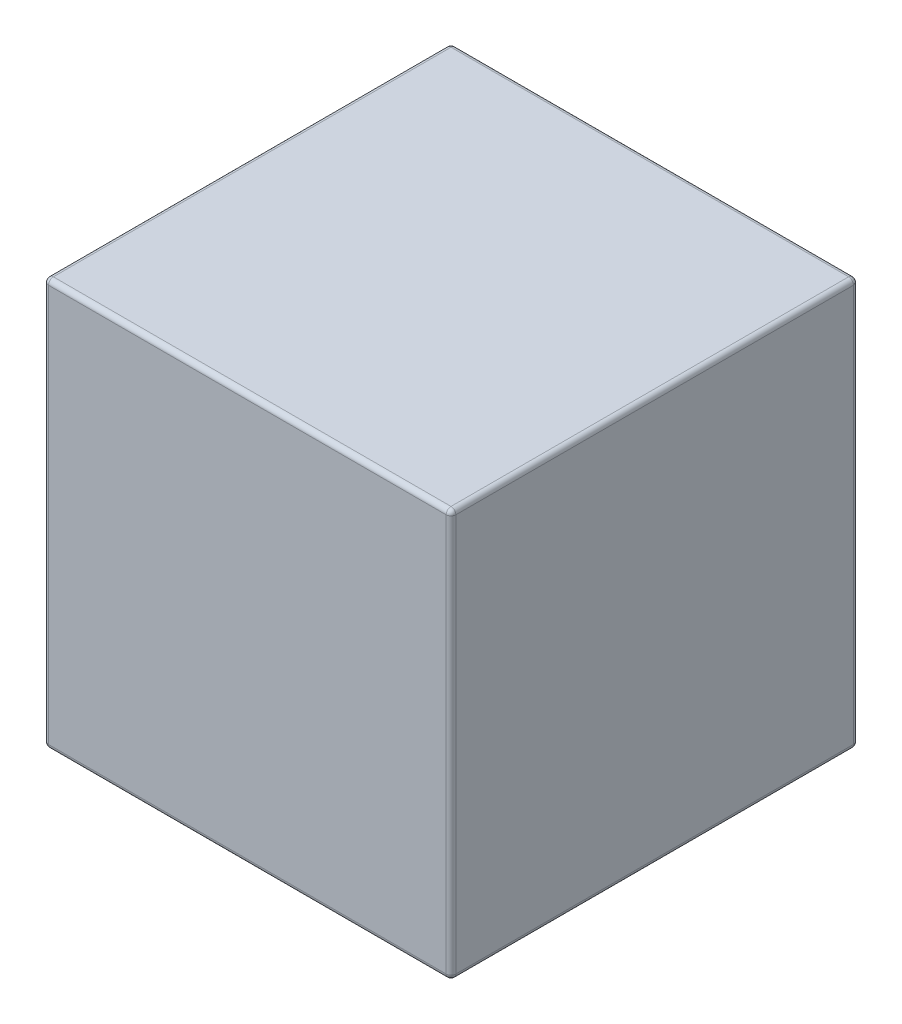
SolidWorks part; units mm, degrees
ref_plane "前视基准面" through (0, 0, 0) normal (0, 0, 1) x (1, 0, 0)
ref_plane "上视基准面" through (0, 0, 0) normal (0, 1, 0) x (1, 0, 0)
ref_plane "右视基准面" through (0, 0, 0) normal (1, 0, 0) x (0, 0, -1)
sketch "草图1" plane through (0, 0, 0) normal (0, 0, 1) x (1, 0, 0)
  line L1 (21, -21) -> (-21, -21)
  line L2 (21, -21) -> (21, 21)
  line L3 (21, 21) -> (-21, 21)
  line L4 (-21, -21) -> (-21, 21)
  line L5 (21, -21) -> (-21, 21) construction
  line L6 (21, 21) -> (-21, -21) construction
  point P0 (0, 0)
  dimension "D1" = 42
  dimension "D2" = 42
extrude "凸台-拉伸1" add sketch "草图1" along normal blind 42
fillet "圆角1" radius 0.5 12 edges at (-21, 21, 21) (0, 21, 42) (-21, 0, 42) (-21, -21, 21) (0, -21, 42) (0, -21, 0) (0, 21, 0) (-21, 0, 0) (21, -21, 21) (21, 0, 42) (21, 21, 21) (21, 0, 0)
